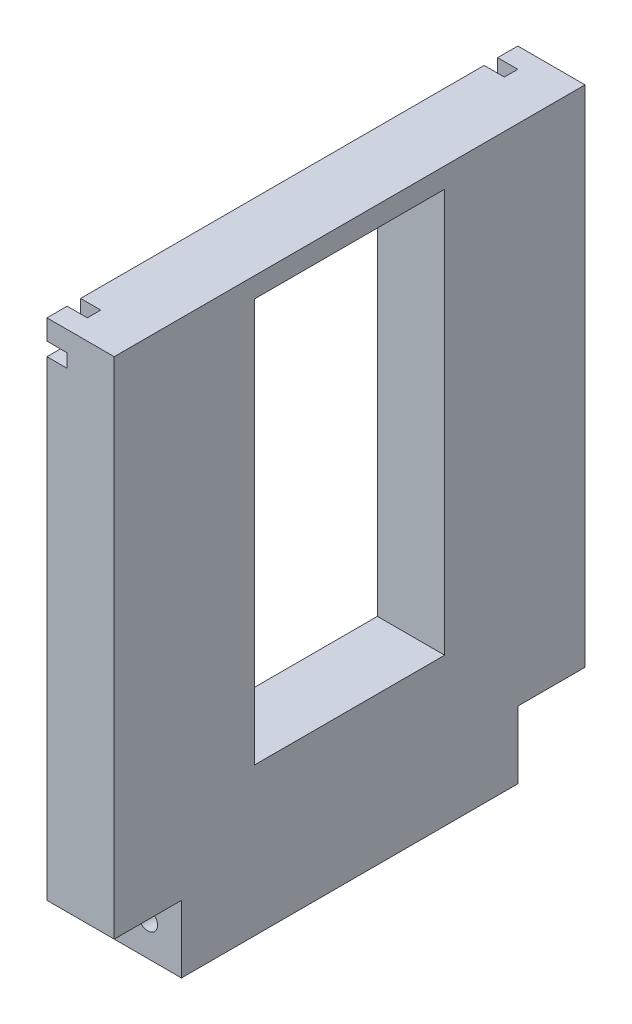
SolidWorks part; units mm, degrees
ref_plane "Alzado" through (0, 0, 0) normal (0, 0, 1) x (1, 0, 0)
ref_plane "Planta" through (0, 0, 0) normal (0, 1, 0) x (1, 0, 0)
ref_plane "Vista lateral" through (0, 0, 0) normal (1, 0, 0) x (0, 0, -1)
sketch "Croquis1" plane through (0, 0, 0) normal (0, 1, 0) x (1, 0, 0)
  line L1 (-5, 35) -> (5, 35)
  line L2 (-5, 35) -> (-5, -35)
  line L3 (-5, -35) -> (5, -35)
  line L4 (5, 35) -> (5, -35)
  line L5 (-5, 35) -> (5, -35) construction
  line L6 (-5, -35) -> (5, 35) construction
  point P0 (0, 0)
  dimension "D1" = 10
  dimension "D2" = 70
extrude "Saliente-Extruir1" add sketch "Croquis1" along normal blind 10
sketch "Croquis8" plane through (0, 10, 0) normal (0, 1, 0) x (1, 0, 0)
  line L0 (-5, -35) -> (5, -35) construction
  line L1 (5, 35) -> (-5, 35)
  line L2 (5, 35) -> (5, -35)
  line L3 (5, -35) -> (-5, -35)
  line L4 (-5, 35) -> (-5, -35)
  dimension "D1" = 10
extrude "Saliente-Extruir3" add sketch "Croquis8" along normal blind 75
sketch "Croquis9" plane through (-5, 0, 0) normal (-1, 0, 0) x (0, 0, 1)
  line L0 (-35, 85) -> (35, 85) construction
  line L1 (-32, 85) -> (-30, 85)
  line L2 (-32, 85) -> (-32, 10)
  line L3 (-32, 10) -> (-30, 10)
  line L4 (-30, 85) -> (-30, 10)
  line L6 (-35, 85) -> (-35, 0) construction
  dimension "D1" = 2
  dimension "D2" = 3
  dimension "D3" = 75
extrude "Cortar-Extruir4" cut sketch "Croquis9" against normal blind 3
mirror "Simetría2" about plane through (0, 0, 0) normal (0, 0, 1) of "Cortar-Extruir4"
sketch "Croquis10" plane through (-5, 0, 0) normal (-1, 0, 0) x (0, 0, 1)
  line L0 (-35, 85) -> (-35, 0) construction
  line L1 (-35, 82) -> (35, 82)
  line L2 (-35, 82) -> (-35, 80)
  line L3 (-35, 80) -> (35, 80)
  line L4 (35, 82) -> (35, 80)
  line L5 (35, 85) -> (35, 0) construction
  line L6 (-30, 85) -> (30, 85) construction
  dimension "D1" = 2
  dimension "D2" = 3
extrude "Cortar-Extruir5" cut sketch "Croquis10" against normal blind 3
sketch "Croquis11" plane through (-5, 0, 0) normal (-1, 0, 0) x (0, 0, 1)
  line L1 (-14.125, 82) -> (14.125, 82)
  line L2 (-14.125, 82) -> (-14.125, 22)
  line L3 (-14.125, 22) -> (14.125, 22)
  line L4 (14.125, 82) -> (14.125, 22)
  line L5 (-14.125, 82) -> (14.125, 22) construction
  line L6 (-14.125, 22) -> (14.125, 82) construction
  line L7 (-30, 10) -> (-30, 80) construction
  line L8 (-30, 85) -> (30, 85) construction
  point P0 (0, 52)
  dimension "D1" = 30
  dimension "D2" = 33
  dimension "D3" = 60
  dimension "D4" = 28.25
extrude "Cortar-Extruir6" cut sketch "Croquis11" against normal up to next
sketch "Croquis16" plane through (-5, 0, 0) normal (-1, 0, 0) x (0, 0, 1)
  line L0 (-35, 80) -> (-35, 0) construction
  line L1 (-20, 10) -> (-10, 10)
  line L2 (-20, 10) -> (-20, 15)
  line L3 (-20, 15) -> (-10, 15)
  line L4 (-10, 10) -> (-10, 15)
  line L5 (-32, 10) -> (-30, 10) construction
  point P8 (-31, 10)
  dimension "D1" = 15
  dimension "D2" = 10
  dimension "D3" = 5
  dimension "D4" = 0
extrude "Saliente-Extruir5" add sketch "Croquis16" along normal blind 7
mirror "Simetría5" about plane through (0, 0, 0) normal (0, 0, 1) of "Saliente-Extruir5"
sketch "Croquis17" plane through (0, 15, 0) normal (0, 1, 0) x (1, 0, 0)
  line L0 (-12, 20) -> (-5, 20) construction
  line L1 (-12, 10) -> (-12, 20) construction
  circle A0 centre (-8.5, 15) radius 1.435
  dimension "D1" = 2.87
  dimension "D2" = 5
  dimension "D3" = 3.5
extrude "Cortar-Extruir9" cut sketch "Croquis17" against normal up to next (5 mm away)
mirror "Simetría6" about plane through (0, 0, 0) normal (0, 0, 1) of "Cortar-Extruir9"
sketch "Croquis18" plane through (-5, 0, 0) normal (-1, 0, 0) x (0, 0, 1)
  line L1 (-35, 0) -> (-25, 0)
  line L2 (-35, 0) -> (-35, 10)
  line L3 (-35, 10) -> (-25, 10)
  line L4 (-25, 0) -> (-25, 10)
  dimension "D1" = 10
  dimension "D2" = 10
extrude "Cortar-Extruir10" cut sketch "Croquis18" against normal up to next (10 mm away)
mirror "Simetría7" about plane through (0, 0, 0) normal (0, 0, 1) of "Cortar-Extruir10"
sketch "Croquis19" plane through (0, 0, -25) normal (0, 0, -1) x (-1, 0, 0)
  line L0 (-5, 0) -> (5, 0) construction
  line L1 (5, 0) -> (5, 10) construction
  circle A0 centre (0, 5) radius 1.435
  point P6 (5, 5)
  dimension "D1" = 2.87
  dimension "D2" = 5
  dimension "D3" = 5
extrude "Cortar-Extruir11" cut sketch "Croquis19" against normal blind 10
mirror "Simetría8" about plane through (0, 0, 0) normal (0, 0, 1) of "Cortar-Extruir11"
